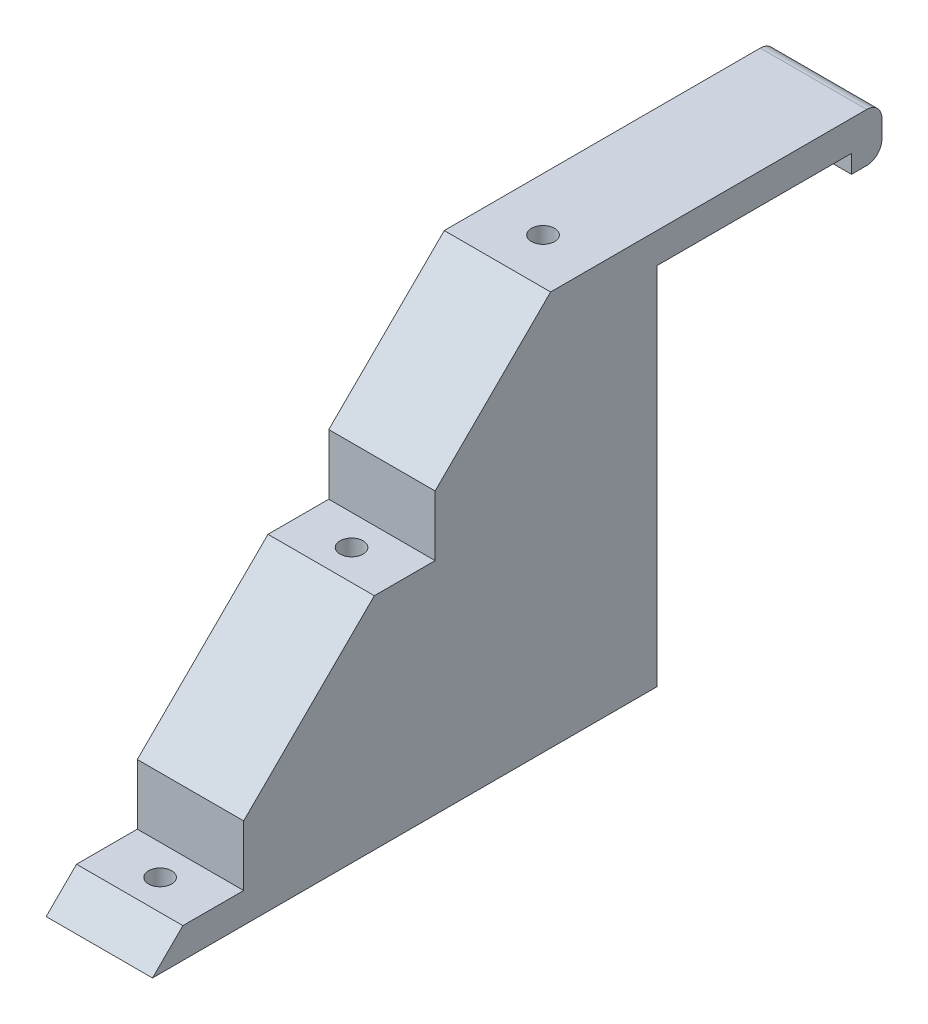
SolidWorks part; units mm, degrees
material "6061-T6 (SS)"
ref_plane "Front Plane" through (0, 0, 0) normal (0, 0, 1) x (1, 0, 0)
ref_plane "Top Plane" through (0, 0, 0) normal (0, 1, 0) x (1, 0, 0)
ref_plane "Right Plane" through (0, 0, 0) normal (1, 0, 0) x (0, 0, -1)
sketch "Sketch1" plane through (0, 0, 0) normal (1, 0, 0) x (0, 0, -1)
  line L0 (-22.225, 6.35) -> (0, 6.35)
  line L2 (0, 6.35) -> (46.99, 6.35)
  line L3 (46.99, 6.35) -> (46.99, -3.81)
  line L4 (46.99, -3.81) -> (40.64, -3.81)
  line L5 (40.64, -3.81) -> (40.64, 0)
  line L6 (40.64, 0) -> (0, 0)
  line L8 (0, 0) -> (-22.225, 0)
  line L9 (-22.225, 0) -> (-22.225, 6.35)
  dimension "D1" = 22.225
  dimension "D2" = 40.64
  dimension "D5" = 6.35
  dimension "D6" = 6.35
  dimension "D7" = 10.16
extrude "Boss-Extrude1" add sketch "Sketch1" along normal mid plane 22.225
sketch "Sketch3" plane through (0, 0, 0) normal (0, -1, 0) x (1, 0, 0)
  line L0 (11.1125, 22.225) -> (11.1125, -40.64) construction
  line L1 (-11.1125, 22.225) -> (11.1125, 22.225)
  line L2 (-11.1125, 22.225) -> (-11.1125, 0)
  line L3 (-11.1125, 0) -> (11.1125, 0)
  line L4 (11.1125, 22.225) -> (11.1125, 0)
extrude "Boss-Extrude2" add sketch "Sketch3" along normal blind 76.2
sketch "Sketch5" plane through (11.1125, 0, 0) normal (1, 0, 0) x (0, 0, -1)
  line L0 (-22.225, 6.35) -> (-105.41, -76.2)
  line L1 (-105.41, -76.2) -> (-22.225, -76.2)
  line L2 (-22.225, -76.2) -> (-22.225, 6.35)
  line L3 (46.99, -3.81) -> (46.99, 6.35) construction
  dimension "D1" = 152.4
extrude "Boss-Extrude3" add sketch "Sketch5" against normal up to surface (22.225 mm away) up to face at (-11.1125, -18.415, -16.3513)
sketch "Sketch6" plane through (0, -76.2, 0) normal (0, -1, 0) x (1, 0, 0)
  line L0 (0, 105.41) -> (0, 0) construction
  line L1 (-11.1125, 105.41) -> (11.1125, 105.41) construction
  line L2 (-11.1125, 52.705) -> (11.1125, 52.705) construction
  line L3 (-11.1125, 105.41) -> (-11.1125, 0) construction
  line L4 (11.1125, 0) -> (11.1125, 105.41) construction
  circle A0 centre (0, 92.71) radius 2.413
  circle A1 centre (0, 12.7) radius 2.413
  circle A2 centre (0, 52.705) radius 2.413
  point P11 (0, 52.705)
  dimension "D1" = 4.826
  dimension "D2" = 12.7
extrude "Cut-Extrude1" cut sketch "Sketch6" against normal through all
sketch "Sketch7" plane through (-11.1125, 0, 0) normal (-1, 0, 0) x (0, 0, 1)
  line L0 (46.355, -17.5958) -> (46.355, -30.1989)
  line L1 (22.225, 6.35) -> (105.41, -76.2) construction
  line L2 (46.355, -30.1989) -> (59.055, -30.1989)
  line L3 (59.055, -30.1989) -> (46.355, -17.5958)
  line L4 (86.36, -57.2954) -> (86.36, -69.8985)
  line L5 (86.36, -69.8985) -> (99.06, -69.8985)
  line L6 (99.06, -69.8985) -> (86.36, -57.2954)
  line L7 (50.292, -76.2) -> (55.118, -76.2) construction
  line L8 (105.41, -76.2) -> (0, -76.2) construction
  line L9 (50.292, -21.5027) -> (50.292, -76.2) construction
  line L10 (90.297, -76.2) -> (95.123, -76.2) construction
  point P19 (92.71, -76.2)
  point P20 (92.71, -69.8985)
  point P21 (52.705, -76.2)
  point P22 (52.705, -30.1989)
  dimension "D1" = 12.7
  dimension "D2" = 12.7
extrude "Cut-Extrude2" cut sketch "Sketch7" against normal through all both and the other way through all
fillet "Fillet1" radius 3.175 2 edges at (0, -3.81, -46.99) (0, 6.35, -46.99)
sketch "Sketch8" plane through (0, 0, 0) normal (0, 0, -1) x (-1, 0, 0)
  line L0 (11.1125, -76.2) -> (-11.1125, -76.2) construction
  circle A0 centre (0, -52.3875) radius 3.175
  dimension "D1" = 6.35
  dimension "D2" = 23.8125
extrude "Cut-Extrude3" cut sketch "Sketch8" against normal blind 9.525
